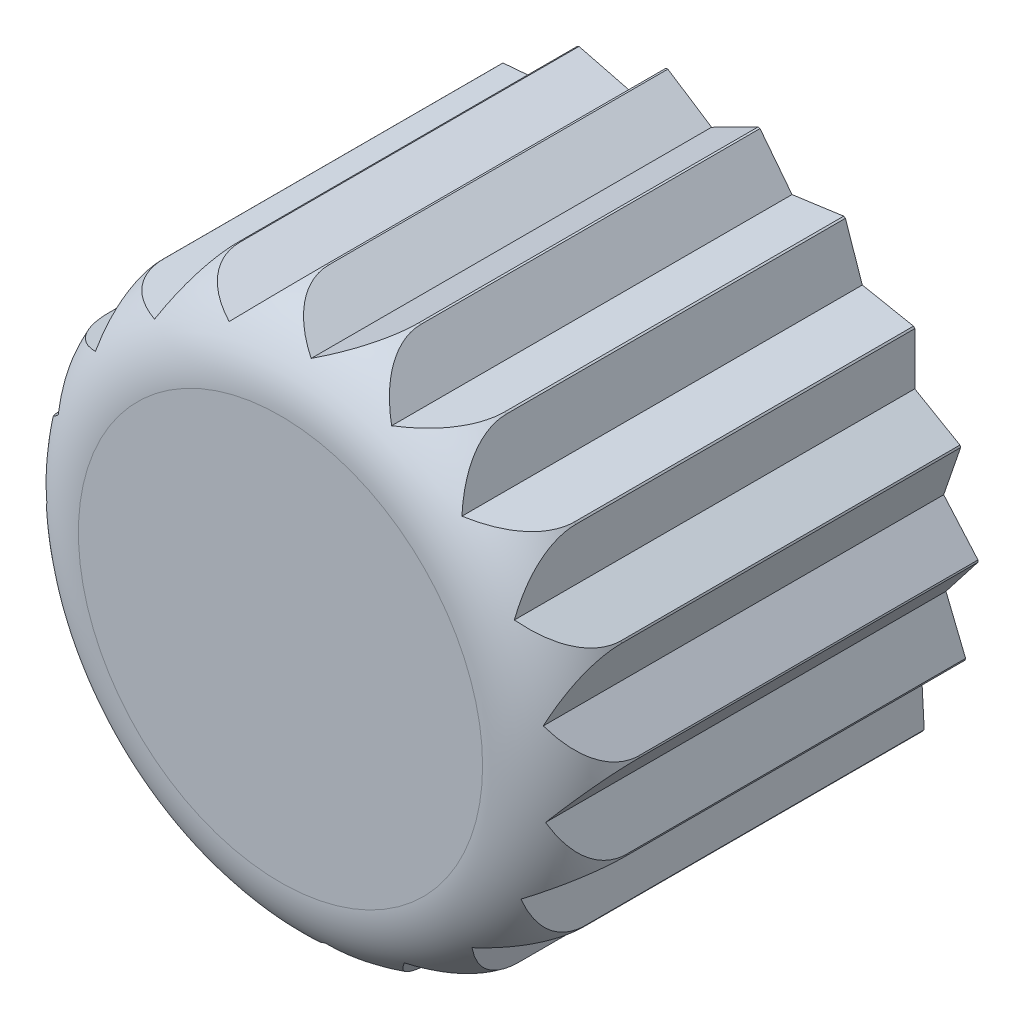
SolidWorks part; units mm, degrees
ref_plane "Front Plane" through (0, 0, 0) normal (0, 0, 1) x (1, 0, 0)
ref_plane "Top Plane" through (0, 0, 0) normal (0, 1, 0) x (1, 0, 0)
ref_plane "Right Plane" through (0, 0, 0) normal (1, 0, 0) x (0, 0, -1)
sketch "Sketch2" plane through (0, 0, 0) normal (0, 0, 1) x (1, 0, 0)
  circle A0 centre (0, 0) radius 5.375
  dimension "D1" = 10.75
extrude "Boss-Extrude1" add sketch "Sketch2" along normal blind 2
sketch "Sketch3" plane through (0, 0, 0) normal (0, 0, -1) x (-1, 0, 0)
  circle A1 centre (0, 0) radius 5.375 construction
  circle A2 centre (0, 0) radius 3.375
  circle A3 centre (0, 0) radius 3.375
  circle A4 centre (0, 0) radius 5.375
  dimension "D1" = 2
extrude "Boss-Extrude2" add sketch "Sketch3" along normal blind 6
fillet "Fillet1" radius 1.5 1 edges at (5.375, 0, 2)
sketch "Sketch4" plane through (0, 0, 2) normal (0, 0, 1) x (1, 0, 0)
  line L0 (5.0404, 1.8669) -> (4.7157, 0.9211)
  line L1 (4.1611, 3.4024) -> (4.1611, 2.4024)
  line L2 (4.1611, 2.4024) -> (5.0271, 1.9024)
  line L3 (4.7157, 0.9211) -> (5.3724, 0.167)
  line L4 (5.3734, 0.1292) -> (4.7592, -0.66)
  line L5 (4.7592, -0.66) -> (5.1355, -1.5864)
  line L6 (5.1242, -1.6226) -> (4.2871, -2.1695)
  line L7 (4.2871, -2.1695) -> (4.3422, -3.168)
  line L8 (4.3198, -3.1985) -> (3.3504, -3.444)
  line L9 (3.3504, -3.444) -> (3.0782, -4.4062)
  line L10 (3.0471, -4.4278) -> (2.0506, -4.3452)
  line L11 (2.0506, -4.3452) -> (1.4808, -5.167)
  line L12 (1.4443, -5.1773) -> (0.5286, -4.7756)
  line L13 (0.5286, -4.7756) -> (-0.2772, -5.3678)
  line L14 (-0.315, -5.3658) -> (-1.0507, -4.6885)
  line L15 (-1.0507, -4.6885) -> (-2.0051, -4.987)
  line L16 (-2.0402, -4.9728) -> (-2.5161, -4.0933)
  line L17 (-2.5161, -4.0933) -> (-3.5158, -4.0657)
  line L18 (-3.5443, -4.0409) -> (-3.7089, -3.0545)
  line L19 (-3.7089, -3.0545) -> (-4.6454, -2.7039)
  line L20 (-4.6643, -2.6711) -> (-4.4997, -1.6847)
  line L21 (-4.4997, -1.6847) -> (-5.2716, -1.049)
  line L22 (-5.2789, -1.0119) -> (-4.8029, -0.1324)
  line L23 (-4.8029, -0.1324) -> (-5.3266, 0.7195)
  line L24 (-5.3214, 0.757) -> (-4.5857, 1.4343)
  line L25 (-4.5857, 1.4343) -> (-4.8044, 2.4101)
  line L26 (-4.7873, 2.4439) -> (-3.8715, 2.8456)
  line L27 (-3.8715, 2.8456) -> (-3.7615, 3.8395)
  line L28 (-3.7344, 3.8659) -> (-2.7378, 3.9485)
  line L29 (-2.7378, 3.9485) -> (-2.311, 4.8528)
  line L30 (-2.2768, 4.869) -> (-1.3074, 4.6235)
  line L31 (-1.3074, 4.6235) -> (-0.6101, 5.3403)
  line L32 (-0.5725, 5.3444) -> (0.2647, 4.7975)
  line L33 (0.2647, 4.7975) -> (1.1569, 5.249)
  line L34 (1.1939, 5.2407) -> (1.8081, 4.4516)
  line L35 (1.8081, 4.4516) -> (2.7986, 4.5889)
  line L36 (2.8308, 4.5691) -> (3.1555, 3.6233)
  line L37 (3.1555, 3.6233) -> (4.137, 3.4316)
  circle A0 centre (0, 0) radius 5.375 construction
  circle A1 centre (0, 0) radius 5.375
  circle A2 centre (0, 0) radius 3.875
  circle A3 centre (0, 0) radius 3.875
  point P0 (0, 0)
  point P65 (0, 0)
  dimension "D1" = 120
  dimension "D2" = 1
  dimension "D3" = 0
  dimension "D4" = 19
extrude "Cut-Extrude1" cut sketch "Sketch4" against normal up to surface (8 mm away) contours L29 A1 L28 | L31 A1 L30 | L27 A1 L26 | L25 A1 L24 | L23 A1 L22 | L21 A1 L20 | L19 A1 L18 | L17 A1 L16 | L15 A1 L14 | L13 A1 L12 | L11 A1 L10 | L9 A1 L8 | L7 A1 L6 | L5 A1 L4 | L3 A1 L0 | L2 A1 L1 | L37 A1 L36 | L35 A1 L34 | L33 A1 L32 up to face at (-5.375, 0, -6)
